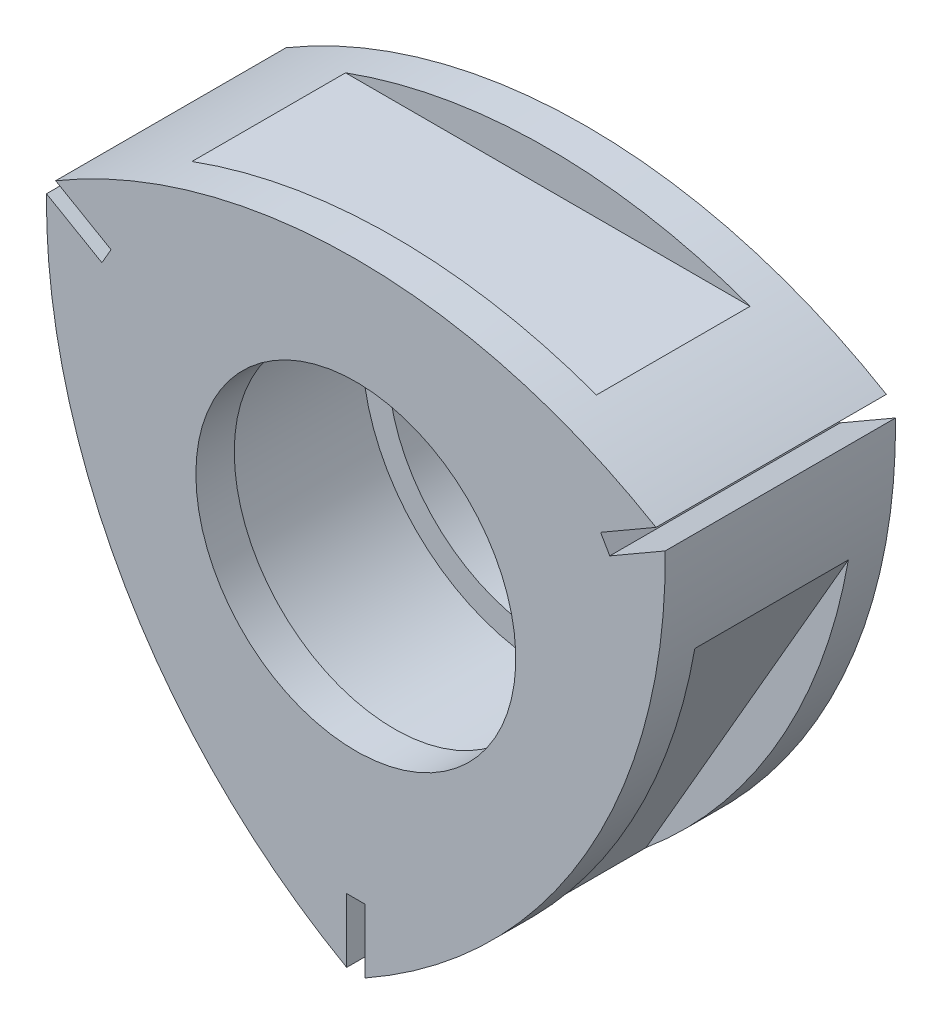
SolidWorks part; units mm, degrees
extrude "Base-Extrude" add sketch "rotor profile" along normal blind 18
sketch "rotor profile" plane through (0, 0, 0) normal (0, 0, 1) x (1, 0, 0)
  line L0 (0, -50.4) -> (0, 0) construction
  line L1 (0, 0) -> (29.8559, 17.2373) construction
  line L2 (0, 0) -> (-26.1316, 15.0871) construction
  line L3 (0, 0) -> (-33.0839, -19.101) construction
  line L4 (0, 0) -> (36.0621, -20.8205) construction
  line L5 (0, 0) -> (0, 28.1893) construction
  line L6 (-23.8157, 13.75) -> (-23.4583, 14.369) construction
  line L7 (-23.8157, 13.75) -> (-24.1731, 13.131) construction
  line L8 (-24.1731, 13.131) -> (-22.1812, 11.981)
  line L9 (-23.4583, 14.369) -> (-21.4664, 13.219)
  line L10 (-19.4856, 11.25) -> (-19.1282, 11.869)
  line L11 (-19.4856, 11.25) -> (-19.843, 10.631)
  line L12 (23.8157, 13.75) -> (23.4583, 14.369) construction
  line L13 (23.8157, 13.75) -> (24.1731, 13.131) construction
  line L14 (19.4856, 11.25) -> (19.843, 10.631)
  line L15 (19.4856, 11.25) -> (19.1282, 11.869)
  line L16 (23.4583, 14.369) -> (19.1282, 11.869)
  line L17 (24.1731, 13.131) -> (19.843, 10.631)
  line L18 (0, -27.5) -> (0.7148, -27.5) construction
  line L19 (0, -27.5) -> (-0.7148, -27.5) construction
  line L20 (0, -22.5) -> (0.7148, -22.5)
  line L21 (0, -22.5) -> (-0.7148, -22.5)
  line L22 (-0.7148, -27.5) -> (-0.7148, -22.5)
  line L23 (0.7148, -27.5) -> (0.7148, -22.5)
  line L24 (-22.1812, 11.981) -> (-19.843, 10.631)
  line L25 (-21.4664, 13.219) -> (-19.1282, 11.869)
  arc A0 (18.0133, -10.4) -> (24.1731, 13.131) centre (-21.8238, 12.6) ccw
  arc A1 (0, 20.8) -> (-23.4583, 14.369) centre (0, -25.2) ccw
  arc A2 (-18.0133, -10.4) -> (-0.7148, -27.5) centre (21.8238, 12.6) ccw
  arc A3 (0.7148, -27.5) -> (18.0133, -10.4) centre (-21.8238, 12.6) ccw
  arc A4 (23.4583, 14.369) -> (0, 20.8) centre (0, -25.2) ccw
  arc A5 (-18.0133, -10.4) -> (-24.1731, 13.131) centre (21.8238, 12.6) cw
  point P6 (-18.0133, -10.4)
  point P8 (0, 0)
  point P9 (18.0133, -10.4)
  point P10 (0, -25.2)
  point P13 (0, -22.5)
  point P15 (21.8238, 12.6)
  point P18 (19.4856, 11.25)
  point P20 (-21.8238, 12.6)
  point P23 (0, 20.8)
  point P27 (0, -27.5)
  point P28 (-23.8157, 13.75)
  point P29 (23.8157, 13.75)
  point P30 (-19.4856, 11.25)
  dimension "D6" = 46
  dimension "D4" = 46
  dimension "D9" = 27.5
  dimension "D10" = 27.5
  dimension "D3" = 20.8
  dimension "D7" = 46
  dimension "D8" = 60
  dimension "D11" = 27.5
  dimension "D1" = 20.8
  dimension "D13" = 46
  dimension "D16" = 46
  dimension "D18" = 46
  dimension "D5" = 60
  dimension "D12" = 22.5
  dimension "D14" = 1.4296
  dimension "D15" = 22.5
  dimension "D17" = 22.5
  dimension "D19" = 1.4296
  dimension "D20" = 1.4296
  dimension "D21" = 20.8
extrude "Cut-Extrude1" cut sketch "combustion chamber profile" against normal blind 12
sketch "combustion chamber profile" plane through (0, 0, 3) normal (0, 0, -1) x (-1, 0, 0)
  line L0 (0, 0) -> (-15.5885, -9) construction
  line L1 (18, 21) -> (18, 18)
  line L2 (-18, 21) -> (18, 21)
  line L3 (-18, 18) -> (-18, 21)
  line L4 (0, 18) -> (-18, 18)
  line L5 (0, 0) -> (0, 18) construction
  line L6 (-9.1865, -26.0885) -> (-27.1865, 5.0885)
  line L7 (-27.1865, 5.0885) -> (-24.5885, 6.5885)
  line L8 (-24.5885, 6.5885) -> (-15.5885, -9)
  line L9 (-15.5885, -9) -> (-6.5885, -24.5885)
  line L10 (-6.5885, -24.5885) -> (-9.1865, -26.0885)
  line L11 (18, 18) -> (0, 18)
  line L16 (27.1865, 5.0885) -> (9.1865, -26.0885)
  line L17 (9.1865, -26.0885) -> (6.5885, -24.5885)
  line L18 (6.5885, -24.5885) -> (15.5885, -9)
  line L19 (15.5885, -9) -> (24.5885, 6.5885)
  line L20 (24.5885, 6.5885) -> (27.1865, 5.0885)
  line L21 (0, 0) -> (15.5885, -9) construction
  circle A0 centre (0, 0) radius 14.5
  point P1 (0, 0)
  dimension "D16" = 29
  dimension "D2" = 120
  dimension "D3" = 120
  dimension "D4" = 18
  dimension "D5" = 18
  dimension "D6" = 3
  dimension "D7" = 3
  dimension "D8" = 18
  dimension "D9" = 18
  dimension "D10" = 18
  dimension "D11" = 18
  dimension "D12" = 18
  dimension "D13" = 3
  dimension "D14" = 18
  dimension "D15" = 18
ref_plane "Front" through (0, 0, 0) normal (0, 0, 1) x (1, 0, 0)
ref_plane "Top" through (0, 0, 0) normal (0, 1, 0) x (1, 0, 0)
ref_plane "Right" through (0, 0, 0) normal (1, 0, 0) x (0, 0, -1)
ref_plane "Plane 3mm offest" through (0, 0, 3) normal (0, 0, -1) x (-1, 0, 0)
ref_plane "Plane 18mm offest" through (0, 0, 18) normal (0, 0, -1) x (-1, 0, 0)
sketch "Sketch5" plane through (0, 0, 18) normal (0, 0, -1) x (-1, 0, 0)
  circle A0 centre (0, 0) radius 12.5
  dimension "D1" = 25
sketch "Sketch6" plane through (0, 0, 18) normal (0, 0, -1) x (-1, 0, 0)
  circle A0 centre (0, 0) radius 12.5
extrude "Cut-Extrude5" cut sketch "Sketch6" along normal through all
